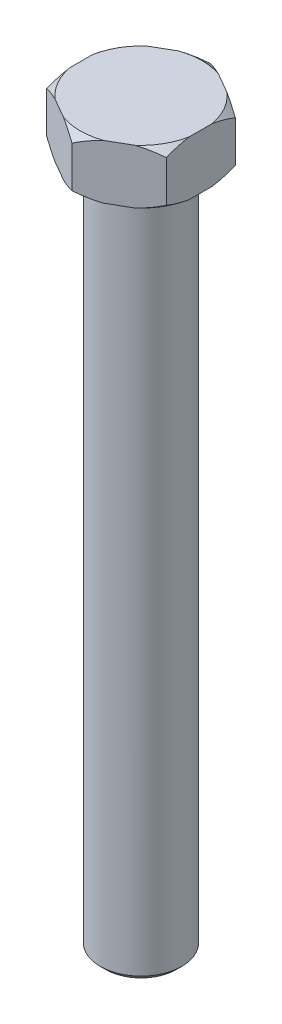
SolidWorks part; units mm, degrees
material "AISI 316 Stainless Steel Sheet (SS)"
ref_plane "Front Plane" through (0, 0, 0) normal (0, 0, 1) x (1, 0, 0)
ref_plane "Top Plane" through (0, 0, 0) normal (0, 1, 0) x (1, 0, 0)
ref_plane "Right Plane" through (0, 0, 0) normal (1, 0, 0) x (0, 0, -1)
sketch "Sketch1" plane through (0, 0, 0) normal (0, 1, 0) x (1, 0, 0)
  line L1 (0, 12.7017) -> (-11, 6.3509)
  line L2 (-11, 6.3509) -> (-11, -6.3509)
  line L3 (-11, -6.3509) -> (0, -12.7017)
  line L4 (0, -12.7017) -> (11, -6.3509)
  line L5 (11, -6.3509) -> (11, 6.3509)
  line L6 (11, 6.3509) -> (0, 12.7017)
  circle A0 centre (0, 0) radius 11 construction
  dimension "D1" = 22
extrude "Boss-Extrude1" add sketch "Sketch1" along normal blind 10
sketch "Sketch2" plane through (0, 0, 0) normal (0, -1, 0) x (1, 0, 0)
  circle A0 centre (0, 0) radius 7.5
  dimension "D1" = 15
extrude "Boss-Extrude2" add sketch "Sketch2" along normal blind 126
cosmetic thread "Cosmetic Thread1" parameters "D1"=20, "D2"=0.911
chamfer "Chamfer1" distance 1 angle 45 1 edges at (0, -126, -7.5)
sketch "Sketch4" plane through (0, 0, 0) normal (1, 0, 0) x (0, 0, -1)
  line L0 (0, 0) -> (0, 10) construction
  line L1 (-6.3509, 10) -> (6.3509, 10) construction
  line L2 (-12.7017, 10) -> (-12.7017, 8.8)
  line L3 (-12.7017, 10) -> (-12.7017, 0) construction
  line L4 (-12.7017, 8.8) -> (-11.2017, 10)
  line L5 (-12.7017, 10) -> (-6.3509, 10) construction
  line L6 (-11.2017, 10) -> (-12.7017, 10)
  line L7 (-12.7017, 0) -> (-12.7017, 1.2)
  line L8 (-12.7017, 1.2) -> (-11.2017, 0)
  line L9 (-12.7017, 0) -> (-6.3509, 0) construction
  line L10 (-11.2017, 0) -> (-12.7017, 0)
  dimension "D1" = 1.5
  dimension "D2" = 1.2
  dimension "D3" = 1.5
  dimension "D4" = 1.2
revolve "Cut-Revolve2" cut sketch "Sketch4" angle 360 about L0
scale "Scale1" scale about centroid uniform scaling yes scale factor 0.18
scale "Scale2" scale about centroid uniform scaling yes scale factor 1.04
